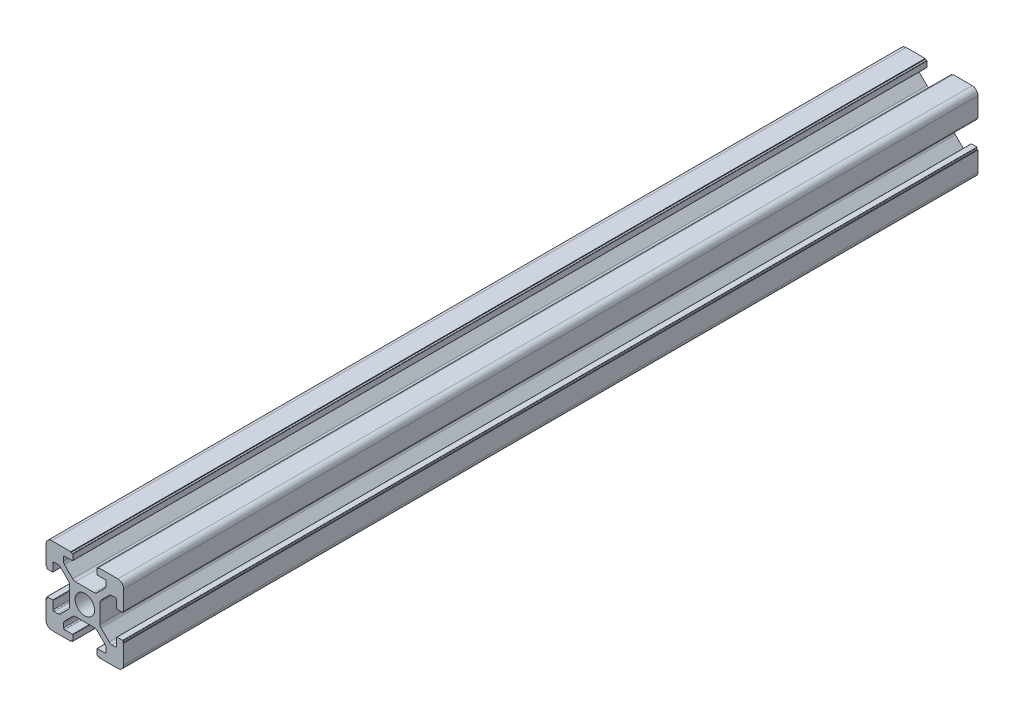
SolidWorks part; units mm, degrees
material "6063-T5"
ref_plane "前视基准面" through (0, 0, 0) normal (0, 0, 1) x (1, 0, 0)
ref_plane "上视基准面" through (0, 0, 0) normal (0, 1, 0) x (1, 0, 0)
ref_plane "右视基准面" through (0, 0, 0) normal (1, 0, 0) x (0, 0, -1)
sketch "草图1" plane through (0, 0, 0) normal (0, 0, 1) x (1, 0, 0)
  line L0 (-1.4389, 10) -> (24.3741, 10) construction
  line L1 (20, 13.6) -> (20, 20)
  line L2 (0, 0) -> (0, 6.4)
  line L3 (0, 20) -> (6.4, 20)
  line L4 (20, 0) -> (20, 6.4)
  line L5 (10, 21.5388) -> (10, -2.4017) construction
  line L6 (6.9, 18.3) -> (6.9, 19.7)
  line L7 (6.8, 18.2) -> (4.8, 18.2)
  line L8 (4.5, 17.9) -> (4.5, 16.9749)
  line L9 (4.7929, 16.2678) -> (6.8678, 14.1929)
  line L10 (7.5749, 13.9) -> (12.4251, 13.9)
  line L11 (6.8, 19.8) -> (6.4, 19.8)
  line L12 (6.4, 19.8) -> (6.4, 20)
  line L13 (0, 13.6) -> (0.2, 13.6)
  line L14 (0.2, 13.6) -> (0.2, 13.2)
  line L15 (0.3, 13.1) -> (1.7, 13.1)
  line L16 (1.8, 13.2) -> (1.8, 15.2)
  line L17 (2.1, 15.5) -> (3.0251, 15.5)
  line L18 (3.7322, 15.2071) -> (5.8071, 13.1322)
  line L19 (6.1, 12.4251) -> (6.1, 7.5749)
  line L20 (13.6, 19.8) -> (13.6, 20)
  line L21 (13.2, 19.8) -> (13.6, 19.8)
  line L22 (13.1, 18.3) -> (13.1, 19.7)
  line L23 (13.2, 18.2) -> (15.2, 18.2)
  line L24 (15.5, 17.9) -> (15.5, 16.9749)
  line L25 (15.2071, 16.2678) -> (13.1322, 14.1929)
  line L26 (0, 6.4) -> (0.2, 6.4)
  line L27 (0.2, 6.4) -> (0.2, 6.8)
  line L28 (0.3, 6.9) -> (1.7, 6.9)
  line L29 (1.8, 6.8) -> (1.8, 4.8)
  line L30 (2.1, 4.5) -> (3.0251, 4.5)
  line L31 (3.7322, 4.7929) -> (5.8071, 6.8678)
  line L32 (13.6, 20) -> (20, 20)
  line L33 (0, 13.6) -> (0, 20)
  line L34 (13.6, 0.2) -> (13.6, 0)
  line L35 (13.2, 0.2) -> (13.6, 0.2)
  line L36 (13.1, 1.7) -> (13.1, 0.3)
  line L37 (13.2, 1.8) -> (15.2, 1.8)
  line L38 (15.5, 2.1) -> (15.5, 3.0251)
  line L39 (15.2071, 3.7322) -> (13.1322, 5.8071)
  line L40 (4.5, 2.1) -> (4.5, 3.0251)
  line L41 (6.8, 1.8) -> (4.8, 1.8)
  line L42 (6.4, 0.2) -> (6.4, 0)
  line L43 (6.8, 0.2) -> (6.4, 0.2)
  line L44 (6.9, 1.7) -> (6.9, 0.3)
  line L45 (4.7929, 3.7322) -> (6.8678, 5.8071)
  line L46 (7.5749, 6.1) -> (12.4251, 6.1)
  line L47 (20, 6.4) -> (19.8, 6.4)
  line L48 (19.8, 6.4) -> (19.8, 6.8)
  line L49 (19.7, 6.9) -> (18.3, 6.9)
  line L50 (18.2, 6.8) -> (18.2, 4.8)
  line L51 (17.9, 4.5) -> (16.9749, 4.5)
  line L52 (16.2678, 4.7929) -> (14.1929, 6.8678)
  line L53 (13.9, 12.4251) -> (13.9, 7.5749)
  line L54 (16.2678, 15.2071) -> (14.1929, 13.1322)
  line L55 (17.9, 15.5) -> (16.9749, 15.5)
  line L56 (18.2, 13.2) -> (18.2, 15.2)
  line L57 (19.7, 13.1) -> (18.3, 13.1)
  line L58 (19.8, 13.6) -> (19.8, 13.2)
  line L59 (20, 13.6) -> (19.8, 13.6)
  line L60 (0, 0) -> (6.4, 0)
  line L61 (13.6, 0) -> (20, 0)
  arc A0 (6.1, 12.4251) -> (5.8071, 13.1322) centre (5.1, 12.4251) ccw
  arc A1 (7.5749, 13.9) -> (6.8678, 14.1929) centre (7.5749, 14.9) cw
  arc A2 (4.5, 16.9749) -> (4.7929, 16.2678) centre (5.5, 16.9749) ccw
  arc A3 (3.7322, 15.2071) -> (3.0251, 15.5) centre (3.0251, 14.5) ccw
  arc A4 (4.5, 17.9) -> (4.8, 18.2) centre (4.8, 17.9) cw
  arc A5 (1.8, 15.2) -> (2.1, 15.5) centre (2.1, 15.2) cw
  arc A6 (0.3, 13.1) -> (0.2, 13.2) centre (0.3, 13.2) cw
  arc A7 (6.9, 19.7) -> (6.8, 19.8) centre (6.8, 19.7) ccw
  arc A8 (1.7, 13.1) -> (1.8, 13.2) centre (1.7, 13.2) ccw
  arc A9 (6.9, 18.3) -> (6.8, 18.2) centre (6.8, 18.3) cw
  arc A10 (13.1, 19.7) -> (13.2, 19.8) centre (13.2, 19.7) cw
  arc A11 (13.1, 18.3) -> (13.2, 18.2) centre (13.2, 18.3) ccw
  arc A12 (15.5, 17.9) -> (15.2, 18.2) centre (15.2, 17.9) ccw
  arc A13 (15.5, 16.9749) -> (15.2071, 16.2678) centre (14.5, 16.9749) cw
  arc A14 (12.4251, 13.9) -> (13.1322, 14.1929) centre (12.4251, 14.9) ccw
  arc A15 (0.3, 6.9) -> (0.2, 6.8) centre (0.3, 6.8) ccw
  arc A16 (1.7, 6.9) -> (1.8, 6.8) centre (1.7, 6.8) cw
  arc A17 (1.8, 4.8) -> (2.1, 4.5) centre (2.1, 4.8) ccw
  arc A18 (3.7322, 4.7929) -> (3.0251, 4.5) centre (3.0251, 5.5) cw
  arc A19 (6.1, 7.5749) -> (5.8071, 6.8678) centre (5.1, 7.5749) cw
  arc A20 (13.1, 0.3) -> (13.2, 0.2) centre (13.2, 0.3) ccw
  arc A21 (13.1, 1.7) -> (13.2, 1.8) centre (13.2, 1.7) cw
  arc A22 (15.5, 2.1) -> (15.2, 1.8) centre (15.2, 2.1) cw
  arc A23 (15.5, 3.0251) -> (15.2071, 3.7322) centre (14.5, 3.0251) ccw
  arc A24 (12.4251, 6.1) -> (13.1322, 5.8071) centre (12.4251, 5.1) cw
  arc A25 (4.5, 2.1) -> (4.8, 1.8) centre (4.8, 2.1) ccw
  arc A26 (6.9, 0.3) -> (6.8, 0.2) centre (6.8, 0.3) cw
  arc A27 (6.9, 1.7) -> (6.8, 1.8) centre (6.8, 1.7) ccw
  arc A28 (4.5, 3.0251) -> (4.7929, 3.7322) centre (5.5, 3.0251) cw
  arc A29 (7.5749, 6.1) -> (6.8678, 5.8071) centre (7.5749, 5.1) ccw
  arc A30 (19.7, 6.9) -> (19.8, 6.8) centre (19.7, 6.8) cw
  arc A31 (18.3, 6.9) -> (18.2, 6.8) centre (18.3, 6.8) ccw
  arc A32 (18.2, 4.8) -> (17.9, 4.5) centre (17.9, 4.8) cw
  arc A33 (16.2678, 4.7929) -> (16.9749, 4.5) centre (16.9749, 5.5) ccw
  arc A34 (13.9, 7.5749) -> (14.1929, 6.8678) centre (14.9, 7.5749) ccw
  arc A35 (13.9, 12.4251) -> (14.1929, 13.1322) centre (14.9, 12.4251) cw
  arc A36 (16.2678, 15.2071) -> (16.9749, 15.5) centre (16.9749, 14.5) cw
  arc A37 (18.2, 15.2) -> (17.9, 15.5) centre (17.9, 15.2) ccw
  arc A38 (18.3, 13.1) -> (18.2, 13.2) centre (18.3, 13.2) cw
  arc A39 (19.7, 13.1) -> (19.8, 13.2) centre (19.7, 13.2) ccw
  circle A40 centre (10, 10) radius 2.5
  point P39 (0.2, 13.1)
  point P42 (6.9, 19.8)
  point P45 (1.8, 13.1)
  point P48 (6.9, 18.2)
  point P66 (10, 13.9)
  point P83 (6.1, 10)
  dimension "D19" = 1
  dimension "D20" = 1
  dimension "D21" = 0.3
  dimension "D22" = 0.1
  dimension "D23" = 5
  dimension "D1" = 20
  dimension "D2" = 20
  dimension "D3" = 10
  dimension "D4" = 10
  dimension "D5" = 1.8
  dimension "D6" = 0.5
  dimension "D7" = 1.6
  dimension "D8" = 3.1
  dimension "D9" = 6.1
  dimension "D10" = 5.5
  dimension "D11" = 3.1
  dimension "D12" = 6.1
  dimension "D13" = 5.5
  dimension "D14" = 1.8
  dimension "D15" = 0.5
  dimension "D16" = 1.5
  dimension "D17" = 45
  dimension "D18" = 1.6
extrude "凸台-拉伸1" add sketch "草图1" along normal blind 220
fillet "圆角1" radius 1.5 4 edges at (20, 0, 110) (0, 0, 110) (0, 20, 110) (20, 20, 110)
sketch "草图2" plane through (0, 0, 0) normal (0, -1, 0) x (1, 0, 0)
  line L0 (10, 220) -> (10, 0) construction
  line L1 (7.5749, 220) -> (12.4251, 220) construction
  line L2 (7.5749, 0) -> (12.4251, 0) construction
  circle A0 centre (10, 110) radius 2
  circle A1 centre (10, 180) radius 2
  circle A2 centre (10, 40) radius 2
  dimension "D1" = 4
  dimension "D2" = 4
  dimension "D3" = 4
  dimension "D4" = 70
  dimension "D5" = 70
extrude "切除-拉伸1" cut sketch "草图2" against normal through all
